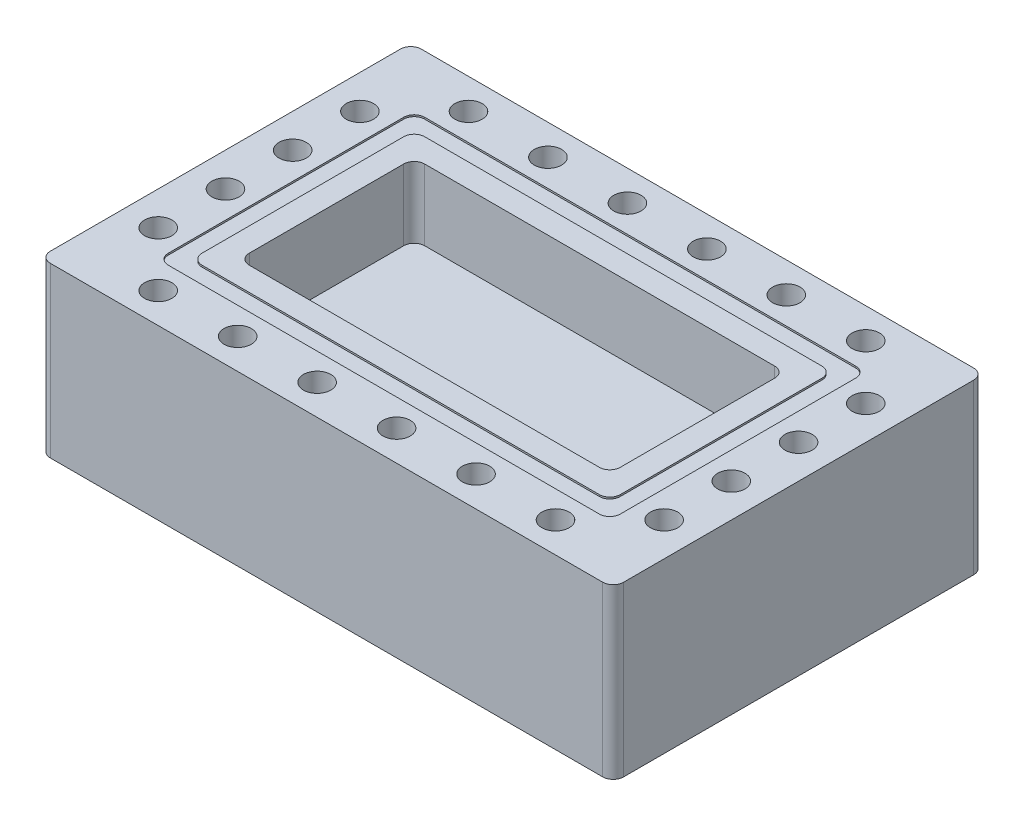
SolidWorks part; units mm, degrees
ref_plane "Front Plane" through (0, 0, 0) normal (0, 0, 1) x (1, 0, 0)
ref_plane "Top Plane" through (0, 0, 0) normal (0, 1, 0) x (1, 0, 0)
ref_plane "Right Plane" through (0, 0, 0) normal (1, 0, 0) x (0, 0, -1)
sketch "Sketch1" plane through (0, 0, 0) normal (0, 1, 0) x (1, 0, 0)
  line L1 (0, 0) -> (85, 0)
  line L2 (0, 0) -> (0, 55)
  line L3 (0, 55) -> (85, 55)
  line L4 (85, 0) -> (85, 55)
  dimension "D1" = 85
  dimension "D2" = 55
extrude "Boss-Extrude1" add sketch "Sketch1" along normal blind 25
sketch "Sketch2" plane through (0, 25, 0) normal (0, 1, 0) x (1, 0, 0)
  line L0 (42.5, 14.5) -> (42.5, 0) construction
  line L1 (15, 40.5) -> (70, 40.5)
  line L2 (15, 40.5) -> (15, 14.5)
  line L3 (15, 14.5) -> (70, 14.5)
  line L4 (70, 40.5) -> (70, 14.5)
  line L5 (0, 0) -> (85, 0) construction
  line L6 (70, 27.5) -> (85, 27.5) construction
  line L7 (85, 0) -> (85, 55) construction
  line L8 (15, 27.5) -> (0, 27.5) construction
  line L9 (0, 55) -> (0, 0) construction
  line L10 (42.5, 40.5) -> (42.5, 55) construction
  line L11 (85, 55) -> (0, 55) construction
  dimension "D1" = 26
  dimension "D2" = 55
extrude "Cut-Extrude1" cut sketch "Sketch2" against normal blind 10.5
fillet "Fillet1" radius 1.55 8 edges at (85, 12.5, -55) (15, 19.75, -40.5) (15, 19.75, -14.5) (70, 19.75, -14.5) (70, 19.75, -40.5) (0, 12.5, -55) (85, 12.5, 0) (0, 12.5, 0)
sketch "Sketch3" plane through (0, 25, 0) normal (0, 1, 0) x (1, 0, 0)
  line L0 (42.5, 14.5) -> (42.5, 11) construction
  line L1 (11.5, 44) -> (73.5, 44)
  line L2 (11.5, 44) -> (11.5, 11)
  line L3 (11.5, 11) -> (73.5, 11)
  line L4 (73.5, 44) -> (73.5, 11)
  line L5 (9, 46.5) -> (76, 46.5)
  line L6 (9, 46.5) -> (9, 8.5)
  line L7 (9, 8.5) -> (76, 8.5)
  line L8 (76, 46.5) -> (76, 8.5)
  line L9 (16.55, 14.5) -> (68.45, 14.5) construction
  line L10 (42.5, 11) -> (42.5, 8.5) construction
  line L11 (42.5, 40.5) -> (42.5, 44) construction
  line L12 (68.45, 40.5) -> (16.55, 40.5) construction
  line L13 (42.5, 44) -> (42.5, 46.5) construction
  line L14 (70, 27.5) -> (73.5, 27.5) construction
  line L15 (70, 16.05) -> (70, 38.95) construction
  line L16 (73.5, 27.5) -> (76, 27.5) construction
  line L17 (15, 27.5) -> (11.5, 27.5) construction
  line L18 (15, 38.95) -> (15, 16.05) construction
  line L19 (11.5, 27.5) -> (9, 27.5) construction
  dimension "D1" = 2.5
  dimension "D2" = 3.5
extrude "Cut-Extrude2" cut sketch "Sketch3" against normal blind 0.25
fillet "Fillet2" radius 1.55 8 edges at (76, 24.875, -46.5) (73.5, 24.875, -44) (73.5, 24.875, -11) (76, 24.875, -8.5) (11.5, 24.875, -11) (9, 24.875, -8.5) (11.5, 24.875, -44) (9, 24.875, -46.5)
sketch "Sketch5" plane through (0, 25, 0) normal (0, 1, 0) x (1, 0, 0)
  line L0 (13.05, 50.5) -> (5, 42.45) construction
  line L1 (5, 42.45) -> (5, 32.4833) construction
  line L2 (5, 32.4833) -> (5, 22.5167) construction
  line L3 (5, 22.5167) -> (5, 12.55) construction
  line L4 (5, 12.55) -> (13.05, 4.5) construction
  line L5 (13.05, 4.5) -> (24.83, 4.5) construction
  line L7 (24.83, 4.5) -> (36.61, 4.5) construction
  line L8 (36.61, 4.5) -> (48.39, 4.5) construction
  line L9 (48.39, 4.5) -> (60.17, 4.5) construction
  line L10 (60.17, 4.5) -> (71.95, 4.5) construction
  line L11 (71.95, 4.5) -> (80, 12.55) construction
  line L12 (80, 12.55) -> (80, 22.5167) construction
  line L13 (80, 22.5167) -> (80, 32.4833) construction
  line L14 (80, 32.4833) -> (80, 42.45) construction
  line L15 (80, 42.45) -> (71.95, 50.5) construction
  line L16 (71.95, 50.5) -> (60.17, 50.5) construction
  line L17 (60.17, 50.5) -> (48.39, 50.5) construction
  line L18 (48.39, 50.5) -> (36.61, 50.5) construction
  line L19 (36.61, 50.5) -> (24.83, 50.5) construction
  line L20 (24.83, 50.5) -> (13.05, 50.5) construction
  line L21 (42.5, 8.5) -> (42.5, 4.5) construction
  line L24 (10.55, 8.5) -> (74.45, 8.5) construction
  line L25 (42.5, 50.5) -> (42.5, 46.5) construction
  line L26 (74.45, 46.5) -> (10.55, 46.5) construction
  line L27 (5, 27.5) -> (9, 27.5) construction
  line L28 (9, 44.95) -> (9, 10.05) construction
  line L29 (76, 27.5) -> (80, 27.5) construction
  line L30 (76, 10.05) -> (76, 44.95) construction
  line L31 (13.05, 11) -> (13.05, 4.5) construction
  line L32 (11.5, 12.55) -> (5, 12.55) construction
  circle A0 centre (5, 42.45) radius 2.025
  circle A1 centre (5, 12.55) radius 2.025
  circle A2 centre (13.05, 4.5) radius 2.025
  circle A3 centre (71.95, 4.5) radius 2.025
  circle A5 centre (24.83, 4.5) radius 2.025
  circle A6 centre (36.61, 4.5) radius 2.025
  circle A7 centre (48.39, 4.5) radius 2.025
  circle A8 centre (60.17, 4.5) radius 2.025
  circle A9 centre (5, 32.4833) radius 2.025
  circle A10 centre (5, 22.5167) radius 2.025
  circle A11 centre (80, 42.45) radius 2.025
  circle A12 centre (80, 12.55) radius 2.025
  circle A13 centre (80, 22.5167) radius 2.025
  circle A14 centre (80, 32.4833) radius 2.025
  circle A15 centre (13.05, 50.5) radius 2.025
  circle A16 centre (24.83, 50.5) radius 2.025
  circle A17 centre (36.61, 50.5) radius 2.025
  circle A18 centre (48.39, 50.5) radius 2.025
  circle A19 centre (60.17, 50.5) radius 2.025
  circle A20 centre (71.95, 50.5) radius 2.025
  dimension "D2" = 4.05
  dimension "D1" = 4
extrude "Cut-Extrude4" cut sketch "Sketch5" against normal through all
